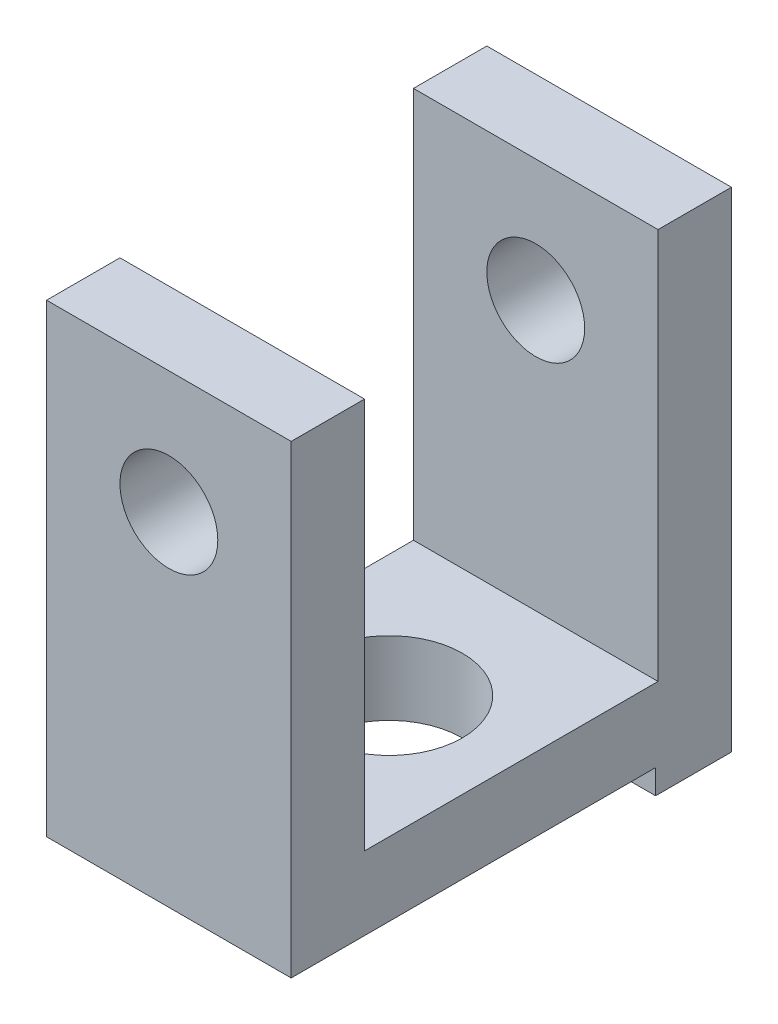
SolidWorks part; units mm, degrees
ref_plane "前视基准面" through (0, 0, 0) normal (0, 0, 1) x (1, 0, 0)
ref_plane "上视基准面" through (0, 0, 0) normal (0, 1, 0) x (1, 0, 0)
ref_plane "右视基准面" through (0, 0, 0) normal (1, 0, 0) x (0, 0, -1)
sketch "草图1" plane through (0, 0, 0) normal (0, 1, 0) x (1, 0, 0)
  line L0 (0, 6.75) -> (0, -6.75)
  line L1 (0, 6.75) -> (5, 6.75)
  line L2 (5, 6.75) -> (5, -6.75)
  line L3 (5, -6.75) -> (0, -6.75)
  line L4 (0, 6.75) -> (-5, 6.75)
  line L5 (-5, 6.75) -> (-5, -6.75)
  line L6 (-5, -6.75) -> (0, -6.75)
  line L7 (0, 0) -> (0, -6)
  line L8 (0, -6) -> (0, -9)
  line L9 (0, -9) -> (-5, -9)
  line L10 (-5, -9) -> (-5, -6.75)
  line L11 (0, -9) -> (5, -9)
  line L12 (5, -9) -> (5, -6.75)
  line L13 (-5, 0) -> (5, 0) construction
  line L14 (5, 9) -> (5, 6.75)
  line L15 (0, 9) -> (5, 9)
  line L16 (0, 9) -> (-5, 9)
  line L17 (-5, 9) -> (-5, 6.75)
  circle A0 centre (0, 0) radius 3
  point P6 (0, 0)
extrude "凸台-拉伸2" add sketch "草图1" along normal blind 4 contours A0 L0 L4 L5 L6 L7 | A0 L7 L0 L3 L2 L1 | L10 L9 L8 L6 | L11 L12 L3 L8 | L5 L13 A0 L0 L4 | A0 L13 L2 L1 L0 | L16 L17 L4 L1 L14 L15
sketch "草图3" plane through (0, 4, 0) normal (0, 1, 0) x (1, 0, 0)
  line L0 (-5, -9) -> (-5, -6)
  line L1 (-5, 9) -> (-5, -9) construction
  line L2 (-5, -6) -> (5, -6)
  line L3 (5, 9) -> (5, -9) construction
  line L4 (5, -6) -> (5, -9)
  line L5 (5, -9) -> (-5, -9)
extrude "凸台-拉伸3" add sketch "草图3" along normal blind 16
sketch "草图4" plane through (0, 0, 9) normal (0, 0, 1) x (1, 0, 0)
  line L0 (0, 0) -> (0, 15)
  circle A0 centre (0, 15) radius 2
extrude "切除-拉伸1" cut sketch "草图4" against normal through all
ref_plane "基准面1" through (0, 0, 0) normal (0, 0, 1) x (1, 0, 0)
mirror "镜向1" about plane through (0, 0, 0) normal (0, 0, 1) of "切除-拉伸1", "凸台-拉伸3"
sketch "草图6" plane through (0, 0, 0) normal (0, -1, 0) x (1, 0, 0)
  line L1 (-5, 9) -> (-5, -5.9)
  line L2 (0, 0) -> (-8.3064, 0) construction
  line L4 (-5, -9) -> (-5, 9) construction
  line L14 (-5, -5.9) -> (5, -5.9)
  line L15 (5, -9) -> (5, 9) construction
  line L16 (5, -5.9) -> (5, 9)
  line L17 (-5, 9) -> (5, 9)
  point P5 (-5, 0)
extrude "切除-拉伸2" cut sketch "草图6" against normal blind 1
